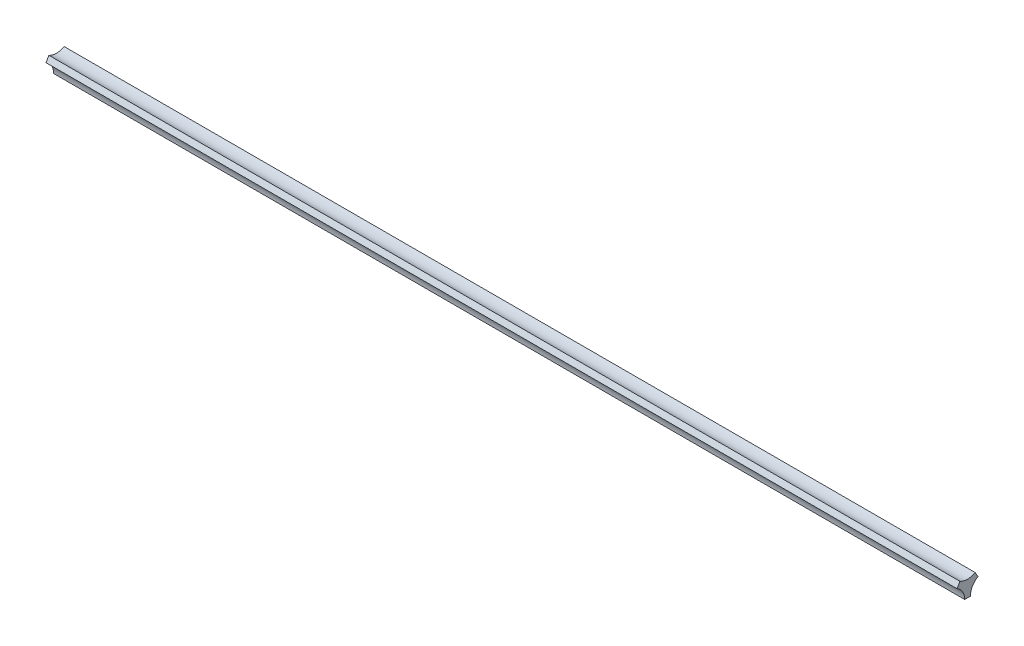
SolidWorks part; units mm, degrees
ref_plane "Front Plane" through (0, 0, 0) normal (0, 0, 1) x (1, 0, 0)
ref_plane "Top Plane" through (0, 0, 0) normal (0, 1, 0) x (1, 0, 0)
ref_plane "Right Plane" through (0, 0, 0) normal (1, 0, 0) x (0, 0, -1)
sketch "Sketch1" plane through (0, 0, 0) normal (1, 0, 0) x (0, 0, -1)
  line L0 (-15, -54.5596) -> (15, -54.5596)
  line L1 (-54.75, 14.2894) -> (-39.75, 40.2702)
  line L2 (39.75, 40.2702) -> (54.75, 14.2894)
  line L3 (0, 0) -> (0, -54.5596) construction
  line L4 (25.651, -14.8096) -> (-47.25, 27.2798) construction
  arc A1 (54.75, 14.2894) -> (15, -54.5596) centre (94.5, -54.5596) ccw
  arc A2 (-15, -54.5596) -> (-54.75, 14.2894) centre (-94.5, -54.5596) ccw
  arc A3 (-39.75, 40.2702) -> (39.75, 40.2702) centre (0, 109.1192) ccw
  dimension "D1" = 60
extrude "Boss-Extrude1" add sketch "Sketch1" along normal mid plane 4760
